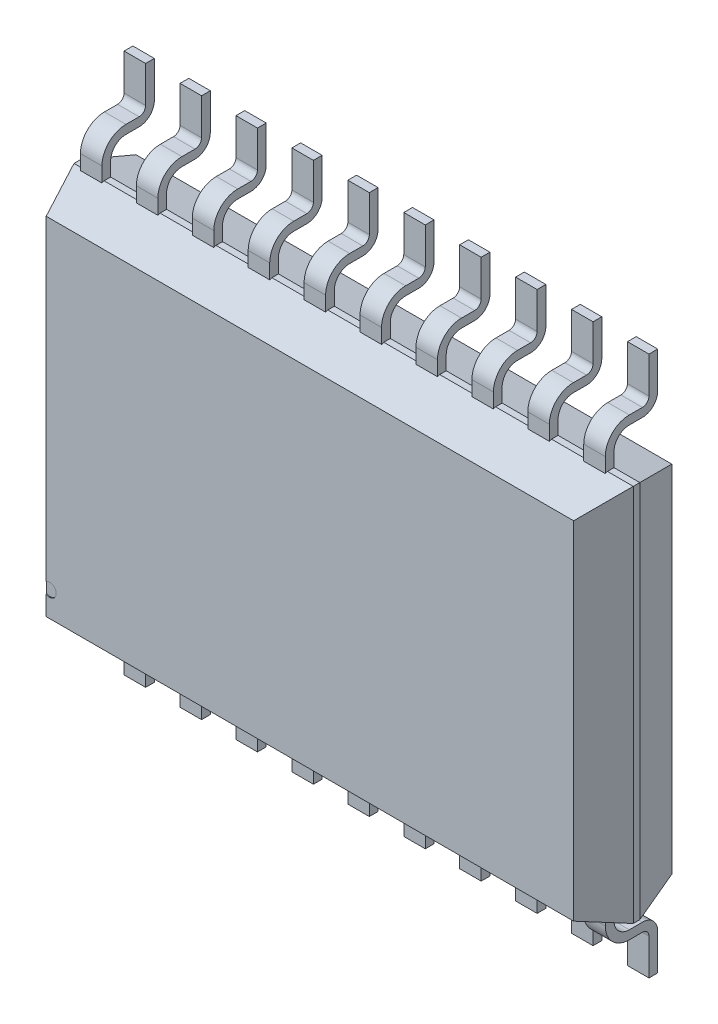
SolidWorks part; units mm, degrees
ref_plane "x/y" through (0, 0, 0) normal (0, 0, 1) x (1, 0, 0)
ref_plane "x/z" through (0, 0, 0) normal (0, 1, 0) x (1, 0, 0)
ref_plane "y/z" through (0, 0, 0) normal (1, 0, 0) x (0, 0, -1)
sketch "Sketch1" plane through (0, 0, 0) normal (0, 0, 1) x (1, 0, 0)
  line L1 (-0.225, 4.7175) -> (6.275, 4.7175)
  line L2 (-0.225, 4.7175) -> (-0.225, 0.3175)
  line L3 (-0.225, 0.3175) -> (6.275, 0.3175)
  line L4 (6.275, 4.7175) -> (6.275, 0.3175)
  dimension "D1" = 4.4
  dimension "D2" = 6.5
  dimension "D3" = 0.225
  dimension "D4" = 0.3175
extrude "Base-Extrude" add sketch "Sketch1" along normal blind 1.0922
chamfer "Chamfer1" distance 0.508 angle 20 4 edges at (-0.225, 2.5175, 1.0922) (3.025, 0.3175, 1.0922) (3.025, 4.7175, 1.0922) (6.275, 2.5175, 1.0922)
chamfer "Chamfer7" distance 0.508 angle 15 4 edges at (3.025, 4.7175, 0) (3.025, 0.3175, 0) (6.275, 2.5175, 0) (-0.225, 2.5175, 0)
sketch "Sketch2" plane through (0, 0, 0) normal (1, 0, 0) x (0, 0, -1)
  line L0 (-0.508, 0.508) -> (-0.508, 0.1553)
  line L1 (0, -0.2003) -> (0, -0.6225)
  line L2 (-0.3302, -0.0225) -> (-0.1778, -0.0225)
  line L3 (-0.5842, 0.3175) -> (-0.508, 0.3175) construction
  arc A0 (-0.3302, -0.0225) -> (-0.508, 0.1553) centre (-0.3302, 0.1553) cw
  arc A1 (-0.1778, -0.0225) -> (0, -0.2003) centre (-0.1778, -0.2003) cw
  point P10 (0, -0.0225)
  dimension "D2" = 0.1778
  dimension "D1" = 0.6
  dimension "D3" = 0.94
extrude "Boss-Extrude-Thin1" add sketch "Sketch2" along normal mid plane 0.25 thin
ref_plane "Plane1" through (0, 2.5175, 0) normal (0, 1, 0) x (-1, 0, 0)
pattern_linear "LPattern1" count 10 spacing 0.65 along (1, 0, 0) of "Boss-Extrude-Thin1"
mirror "Mirror1" about plane through (0, 2.5175, 0) normal (0, 1, 0) of "Boss-Extrude-Thin1", "LPattern1"
sketch "Sketch3" plane through (0, 0, 1.0922) normal (0, 0, 1) x (1, 0, 0)
  circle A0 centre (0, 0.793) radius 0.0764
extrude "Extrude1" cut sketch "Sketch3" against normal blind 0.01
